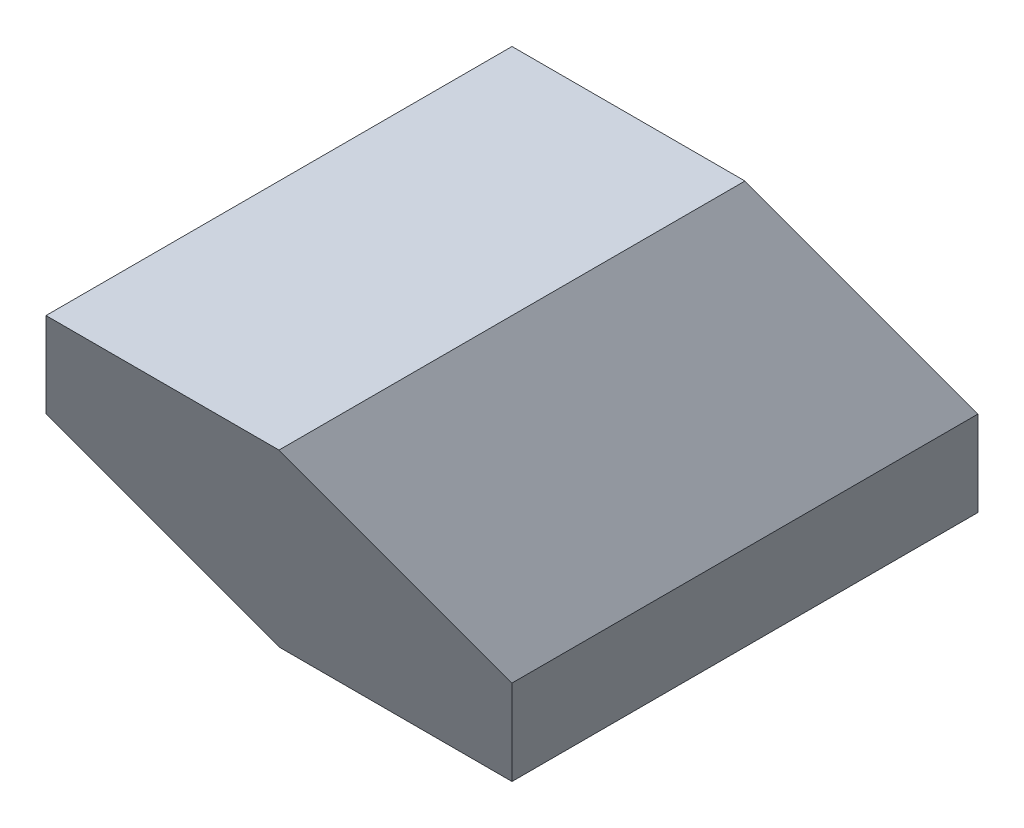
SolidWorks part; units mm, degrees
ref_plane "Front" through (0, 0, 0) normal (0, 0, 1) x (1, 0, 0)
ref_plane "Top" through (0, 0, 0) normal (0, 1, 0) x (1, 0, 0)
ref_plane "Right" through (0, 0, 0) normal (1, 0, 0) x (0, 0, -1)
sketch "Sketch1" plane through (0, 0, 0) normal (0, 0, 1) x (1, 0, 0)
  line L1 (40.4145, 0) -> (20.2073, 35)
  line L2 (20.2073, 35) -> (-20.2073, 35)
  line L3 (-20.2073, 35) -> (-40.4145, 0)
  line L4 (-40.4145, 0) -> (-20.2073, -35)
  line L5 (-20.2073, -35) -> (20.2073, -35)
  line L6 (20.2073, -35) -> (40.4145, 0)
  circle A0 centre (0, 0) radius 35 construction
extrude "Extrude1" add sketch "Sketch1" along normal mid plane 130
sketch "Sketch2" plane through (0, 0, 0) normal (0, 0, 1) x (1, 0, 0)
  line L0 (0, 35) -> (0, -35)
  arc A0 (0, -35) -> (0, 35) centre (0, 0) ccw
revolve "Revolve1" add sketch "Sketch2" angle 360 about L0
sketch "Sketch3" plane through (0, 0, 0) normal (1, 0, 0) x (0, 0, -1)
  line L0 (65, -35) -> (65, 35)
  line L2 (20.2073, 35) -> (60.6218, -35)
  line L3 (65, 35) -> (20.2073, 35)
  line L4 (-60.6218, 35) -> (-20.2073, -35)
  line L5 (-65, 35) -> (-65, -35)
  line L6 (-65, -35) -> (-20.2073, -35)
  line L7 (60.6218, -35) -> (65, -35)
  line L8 (-60.6218, 35) -> (-65, 35)
extrude "Cut-Extrude1" cut sketch "Sketch3" against normal mid plane 90
